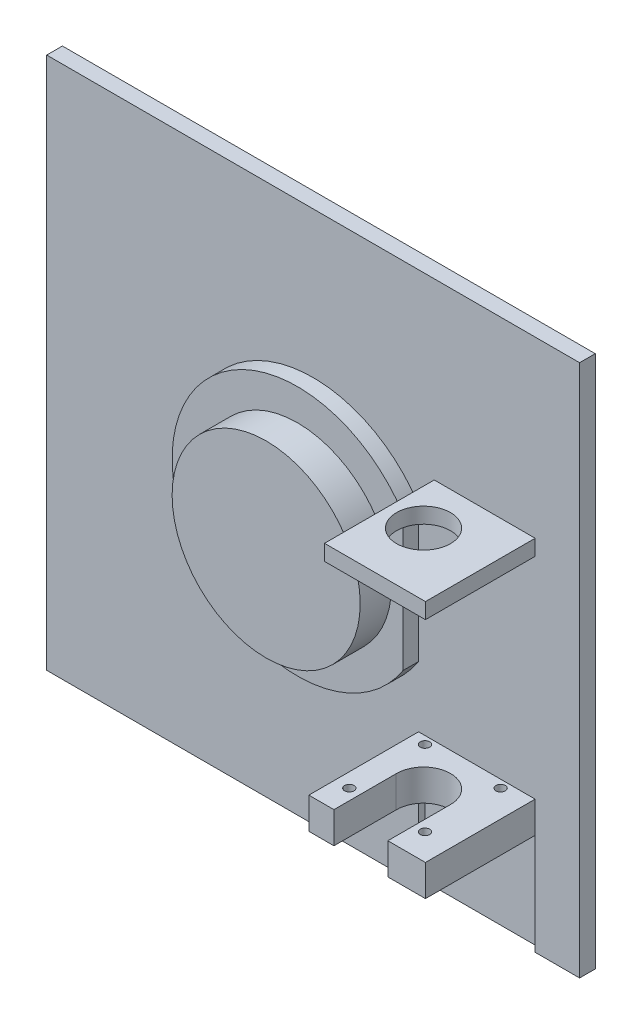
SolidWorks part; units mm, degrees
ref_plane "Front Plane" through (0, 0, 0) normal (0, 0, 1) x (1, 0, 0)
ref_plane "Top Plane" through (0, 0, 0) normal (0, 1, 0) x (1, 0, 0)
ref_plane "Right Plane" through (0, 0, 0) normal (1, 0, 0) x (0, 0, -1)
sketch "Sketch1" plane through (0, 0, 0) normal (0, 0, 1) x (1, 0, 0)
  line L1 (0, 0) -> (215.9, 0)
  line L2 (0, 0) -> (0, 215.9)
  line L3 (0, 215.9) -> (215.9, 215.9)
  line L4 (215.9, 0) -> (215.9, 215.9)
  dimension "D1" = 215.9
  dimension "D2" = 215.9
extrude "Boss-Extrude1" add sketch "Sketch1" along normal blind 12.7
sketch "Sketch2" plane through (0, 0, 12.7) normal (0, 0, 1) x (1, 0, 0)
  line L0 (215.9, 0) -> (215.9, 41.0616)
  line L1 (215.9, 0) -> (215.9, 215.9) construction
  line L2 (215.9, 41.0616) -> (174.2694, 41.0616)
  line L3 (174.2694, 41.0616) -> (197.8914, 41.0616)
  line L4 (197.8914, 41.0616) -> (197.8914, 53.7616)
  line L5 (174.2694, 41.0616) -> (150.6474, 41.0616)
  line L6 (150.6474, 41.0616) -> (150.6474, 53.7616)
  line L7 (150.6474, 53.7616) -> (197.8914, 53.7616)
  dimension "D1" = 41.0616
  dimension "D2" = 41.6306
  dimension "D3" = 90
  dimension "D4" = 23.622
  dimension "D5" = 23.622
  dimension "D6" = 12.7
  dimension "D7" = 12.7
extrude "Boss-Extrude2" add sketch "Sketch2" along normal blind 38.1 contours L5 L6 L7 L4 L3
sketch "Sketch4" plane through (0, 0, 12.7) normal (0, 0, 1) x (1, 0, 0)
  line L0 (197.8914, 41.0616) -> (197.8914, 0)
  line L1 (0, 0) -> (215.9, 0) construction
  line L3 (150.6474, 41.0616) -> (197.8914, 41.0616)
  line L4 (150.6474, 41.0616) -> (150.6474, 0)
  line L5 (150.6474, 0) -> (197.8914, 0)
  line L6 (197.8914, 41.0616) -> (197.8914, 0)
  line M2 (0, 0) -> (215.9, 0)
  line M6 (197.8914, 41.0616) -> (150.6474, 41.0616)
extrude "Cut-Extrude1" cut sketch "Sketch4" against normal blind 8.89 contours L4 L0 M6 M2
sketch "Sketch5" plane through (0, 41.0616, 0) normal (0, -1, 0) x (1, 0, 0)
  line L0 (171.7308, 50.8) -> (171.7308, 3.81) construction
  line L3 (197.8914, 12.7) -> (150.6474, 12.7) construction
  line L4 (171.7307, 12.9655) -> (171.7308, 25.4115) construction
  circle A0 centre (171.7308, 25.4115) radius 10.922
  dimension "D2" = 26.162
  dimension "D3" = 21.844
  dimension "D1" = 12.446
sketch "Sketch6" plane through (0, 0, 12.7) normal (0, 0, 1) x (1, 0, 0)
  line L0 (197.8914, 41.0616) -> (197.8914, 138.9532)
  line L1 (150.6474, 41.0616) -> (150.6474, 215.9)
  line L2 (215.9, 215.9) -> (0, 215.9) construction
  line L4 (197.8914, 138.9532) -> (150.6474, 138.9532)
  line L5 (197.8914, 138.9532) -> (197.8914, 145.3032)
  line L6 (197.8914, 145.3032) -> (150.6474, 145.3032)
  line L7 (150.6474, 138.9532) -> (150.6474, 145.3032)
  dimension "D1" = 97.8916
  dimension "D2" = 6.35
extrude "Boss-Extrude3" add sketch "Sketch6" along normal blind 38.1 contours L5 L6 L1 L4
extrude "Cut-Extrude2" cut sketch "Sketch5" against normal through all contours A0
sketch "Sketch8" plane through (0, 41.0616, 0) normal (0, -1, 0) x (1, 0, 0)
  line L0 (160.812, 25.146) -> (160.812, 50.8)
  line L1 (150.6474, 50.8) -> (197.8914, 50.8) construction
  line L2 (182.6495, 25.146) -> (182.6495, 50.8)
  line L3 (182.6495, 50.8) -> (160.812, 50.8)
  circle A0 centre (171.7308, 25.4115) radius 10.922 construction
  arc A1 (160.812, 25.146) -> (182.6495, 25.146) centre (171.7308, 25.146) cw
  dimension "D1" = 25.654
  dimension "D2" = 25.654
extrude "Cut-Extrude4" cut sketch "Sketch8" against normal blind 38.1
sketch "Sketch9" plane through (0, 0, 12.7) normal (0, 0, 1) x (1, 0, 0)
  line L1 (150.6474, 138.9532) -> (197.8914, 138.9532)
  line L2 (150.6474, 138.9532) -> (150.6474, 53.7616)
  line L3 (150.6474, 53.7616) -> (197.8914, 53.7616)
  line L4 (197.8914, 138.9532) -> (197.8914, 53.7616)
extrude "Cut-Extrude5" cut sketch "Sketch9" against normal blind 6.35
sketch "Sketch10" plane through (0, 41.0616, 0) normal (0, -1, 0) x (1, 0, 0)
  line L0 (171.7308, 25.4115) -> (187.0597, 25.4115) construction
  line L1 (187.0597, 25.4115) -> (187.0597, 9.4984) construction
  line L2 (187.0597, 9.4984) -> (156.4019, 9.4984) construction
  line L4 (156.4019, 9.4984) -> (187.0597, 9.4984)
  line L5 (156.4019, 9.4984) -> (156.4019, 40.1562) construction
  line L6 (156.4019, 40.1562) -> (187.0597, 40.1562) construction
  line L7 (187.0597, 9.4984) -> (187.0597, 40.1562) construction
  circle A0 centre (171.7308, 25.4115) radius 10.922
  circle A1 centre (187.0597, 9.4984) radius 1.905
  circle A2 centre (156.4019, 9.4984) radius 1.905
  circle A3 centre (156.4019, 40.1562) radius 1.905
  circle A4 centre (187.0597, 40.1562) radius 1.905
  point P4 (171.7308, 25.4115)
  point P13 (171.7308, 25.4115)
  dimension "D5" = 3.81
  dimension "D6" = 3.81
  dimension "D7" = 3.81
  dimension "D8" = 3.81
  dimension "D1" = 15.3289
  dimension "D2" = 15.9131
  dimension "D3" = 30.6578
  dimension "D4" = 30.6578
sketch "Sketch12" plane through (0, 0, 12.7) normal (0, 0, 1) x (1, 0, 0)
  line L0 (215.9, 215.9) -> (107.95, 215.9)
  line L1 (215.9, 215.9) -> (0, 215.9) construction
  line L2 (107.95, 215.9) -> (107.95, -4.045) construction
  circle A0 centre (107.95, 105.9275) radius 38.1
  circle A1 centre (107.95, 105.9275) radius 44.45
extrude "Boss-Extrude4" add sketch "Sketch12" along normal blind 12.7 contours A0 L2 | L2 A0
sketch "Sketch13" plane through (0, 0, 12.7) normal (0, 0, 1) x (1, 0, 0)
  circle A0 centre (107.95, 105.9275) radius 47.625
sketch "Sketch14" plane through (150.6474, 0, 0) normal (-1, 0, 0) x (0, 0, 1)
  line L1 (50.8, 145.3032) -> (12.7, 145.3032)
  line L2 (50.8, 145.3032) -> (50.8, 138.9532)
  line L3 (50.8, 138.9532) -> (12.7, 138.9532)
  line L4 (12.7, 145.3032) -> (12.7, 138.9532)
extrude "Cut-Extrude7" cut sketch "Sketch14" against normal blind 6.35
extrude "Cut-Extrude9" cut sketch "Sketch10" against normal blind 12.7
sketch "Sketch15" plane through (0, 0, 12.7) normal (0, 0, 1) x (1, 0, 0)
  line L0 (197.8914, 0) -> (215.9, 0)
  line L1 (215.9, 0) -> (215.9, 215.9)
  line L2 (215.9, 215.9) -> (0, 215.9)
  line L3 (0, 215.9) -> (0, 0)
  line L4 (0, 0) -> (150.6474, 0)
  line L5 (150.6474, 78.4035) -> (150.6474, 0)
  line L6 (150.6474, 138.9532) -> (150.6474, 53.7616) construction
  line L7 (150.6474, 133.4515) -> (150.6474, 138.9532)
  line L8 (150.6474, 138.9532) -> (156.9974, 145.3032)
  line L9 (156.9974, 145.3032) -> (197.8914, 145.3032)
  line L10 (197.8914, 145.3032) -> (197.8914, 0)
  circle A0 centre (107.95, 105.9275) radius 50.8
  arc A1 (150.6474, 133.4515) -> (150.6474, 78.4035) centre (107.95, 105.9275) ccw
  line M3 (150.6474, 41.0616) -> (150.6474, 53.7616)
  line M4 (150.6474, 53.7616) -> (150.6474, 138.9532)
  line M7 (156.9974, 145.3032) -> (197.8914, 145.3032)
  line M8 (197.8914, 145.3032) -> (197.8914, 138.9532)
  line M9 (197.8914, 138.9532) -> (197.8914, 53.7616)
  line M10 (197.8914, 53.7616) -> (197.8914, 41.0616)
  line M11 (197.8914, 41.0616) -> (197.8914, 0)
  line M12 (197.8914, 0) -> (215.9, 0)
  line M13 (215.9, 0) -> (215.9, 215.9)
  line M14 (215.9, 215.9) -> (0, 215.9)
  line M15 (0, 215.9) -> (0, 0)
  line M16 (0, 0) -> (150.6474, 0)
  line M17 (150.6474, 0) -> (150.6474, 41.0616)
  dimension "D1" = 101.6
extrude "Cut-Extrude10" cut sketch "Sketch15" against normal blind 6.35 contours A0 L8 M4 M7 M8 M9 M10 M11 M12 M13 M14 M15 M16 M17 M3
